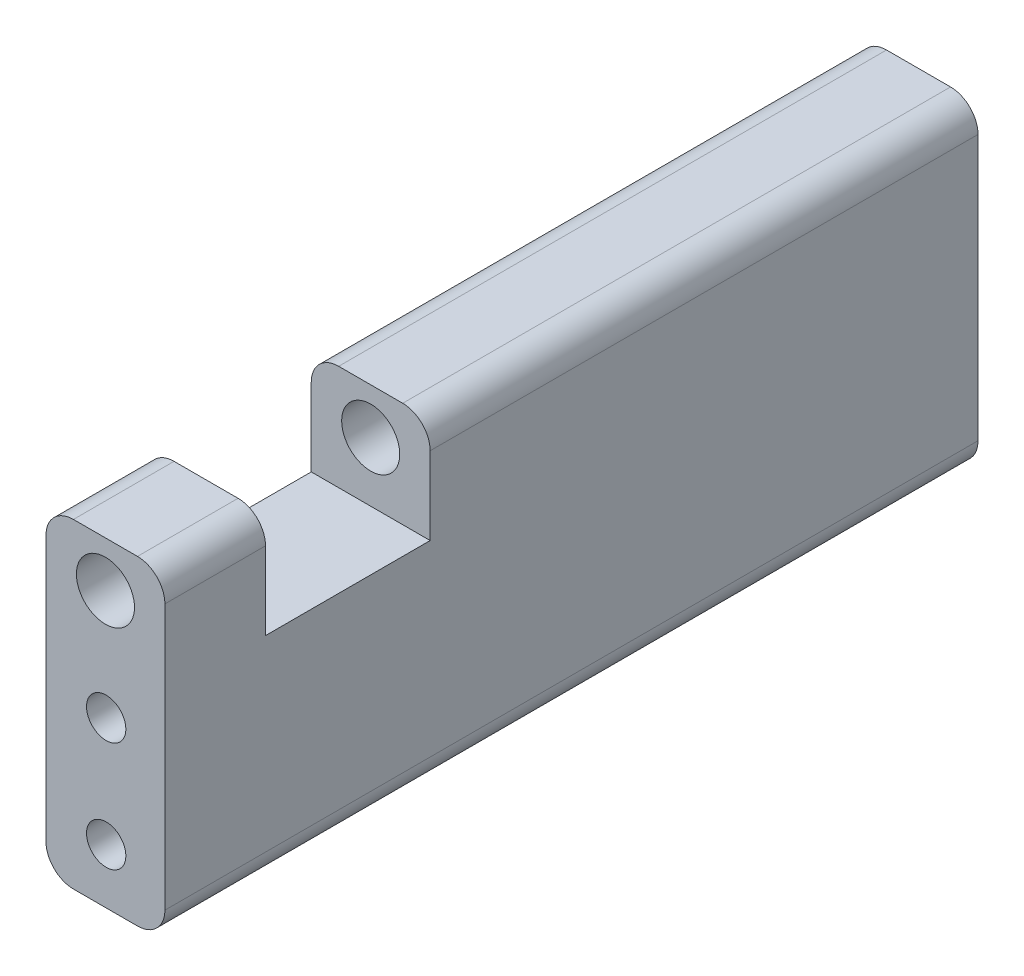
SolidWorks part; units mm, degrees
ref_plane "Front Plane" through (0, 0, 0) normal (0, 0, 1) x (1, 0, 0)
ref_plane "Top Plane" through (0, 0, 0) normal (0, 1, 0) x (1, 0, 0)
ref_plane "Right Plane" through (0, 0, 0) normal (1, 0, 0) x (0, 0, -1)
sketch "Sketch1" plane through (0, 0, 0) normal (0, 0, 1) x (1, 0, 0)
  line L0 (6.5, 0) -> (6.5, 35) construction
  line L5 (0, 0) -> (13, 0)
  line L6 (0, 0) -> (0, 35)
  line L7 (0, 35) -> (13, 35)
  line L8 (13, 0) -> (13, 35)
  circle A0 centre (6.5, 30) radius 3.175
  dimension "D2" = 6.35
  dimension "D1" = 5
  dimension "D3" = 13
  dimension "D4" = 35
extrude "Boss-Extrude1" add sketch "Sketch1" along normal blind 88.9
ref_plane "Plane1" through (0, 0, 68.9) normal (0, 0, 1) x (1, 0, 0)
sketch "Sketch2" plane through (0, 0, 68.9) normal (0, 0, 1) x (1, 0, 0)
  line L0 (0, 35) -> (0, 0) construction
  line L1 (0, 30) -> (0, 35)
  line L2 (0, 35) -> (13, 35)
  line L3 (13, 35) -> (13, 30)
  line L4 (0, 30) -> (0, 23.5)
  line L5 (0, 23.5) -> (13, 23.5)
  line L6 (13, 0) -> (13, 35) construction
  line L7 (13, 23.5) -> (13, 30)
  arc A0 (0, 30) -> (13, 30) centre (6.5, 30) ccw construction
extrude "Cut-Extrude1" cut sketch "Sketch2" against normal mid plane 18
hole_wizard "M4 Clearance Hole1" positions "Sketch3" profile "Sketch6" hole size "M4" standard "ANSI Metric"
sketch "Sketch3" plane through (0, 0, 0) normal (0, 0, -1) x (-1, 0, 0)
  line L0 (0, 0) -> (-13, 0) construction
  point P0 (-6.5792, 18)
  point P2 (-6.5792, 6)
  dimension "D1" = 6
  dimension "D2" = 12
sketch "Sketch6" plane through (6.5792, 18, 0) normal (1, 0, 0) x (0, 1, 0)
  line L0 (0, 0) -> (0, 6.2919)
  line L1 (0, 6.2919) -> (2.15, 5)
  line L2 (2.15, 5) -> (2.15, 0)
  line L5 (2.15, 0) -> (0, 0)
  line L10 (0, 6.2919) -> (-2.15, 5) construction
  line L11 (0, -6.35) -> (0, 107.95) construction
  dimension "Hole Dia." = 4.3
  dimension "Hole Depth" = 5
  dimension "Drill Angle" = 118
hole_wizard "M4 Clearance Hole2" positions "Sketch7" profile "Sketch8" hole size "M4" standard "ANSI Metric"
sketch "Sketch7" plane through (0, 0, 88.9) normal (0, 0, 1) x (1, 0, 0)
  point P0 (6.5792, 18)
  point P3 (6.5792, 6)
sketch "Sketch8" plane through (6.5792, 18, 88.9) normal (1, 0, 0) x (0, -1, 0)
  line L0 (0, 0) -> (0, 6.2919)
  line L1 (0, 6.2919) -> (2.15, 5)
  line L2 (2.15, 5) -> (2.15, 0)
  line L5 (2.15, 0) -> (0, 0)
  line L10 (0, 6.2919) -> (-2.15, 5) construction
  line L11 (0, -6.35) -> (0, 107.95) construction
  dimension "Hole Dia." = 4.3
  dimension "Hole Depth" = 5
  dimension "Drill Angle" = 118
fillet "Fillet1" radius 3 6 edges at (0, 0, 44.45) (13, 0, 44.45) (0, 35, 83.4) (13, 35, 83.4) (0, 35, 29.95) (13, 35, 29.95)
